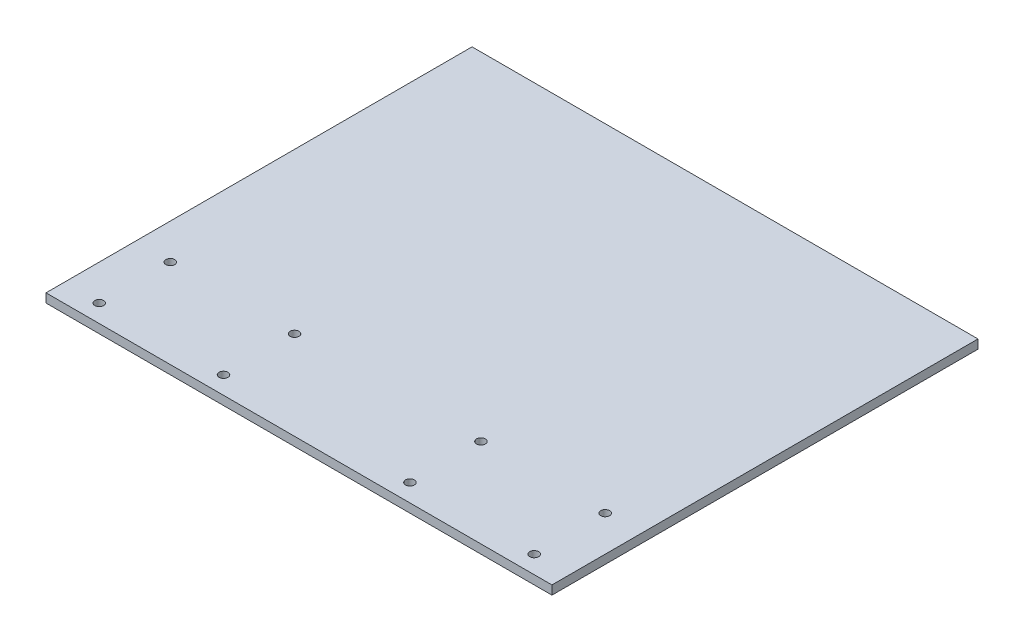
SolidWorks part; units mm, degrees
material "Cast Carbon Steel"
ref_plane "Front Plane" through (0, 0, 0) normal (0, 0, 1) x (1, 0, 0)
ref_plane "Top Plane" through (0, 0, 0) normal (0, 1, 0) x (1, 0, 0)
ref_plane "Right Plane" through (0, 0, 0) normal (1, 0, 0) x (0, 0, -1)
sketch "Sketch1" plane through (0, 0, 0) normal (0, 1, 0) x (1, 0, 0)
  line L1 (-295.5989, 609.6) -> (428.3011, 609.6)
  line L2 (-295.5989, 609.6) -> (-295.5989, 0)
  line L3 (-295.5989, 0) -> (428.3011, 0)
  line L4 (428.3011, 609.6) -> (428.3011, 0)
  dimension "D1" = 723.9
  dimension "D2" = 609.6
  dimension "D4" = 295.5989
extrude "Boss-Extrude1" add sketch "Sketch1" along normal blind 12.7
sketch "Sketch2" plane through (0, 12.7, 0) normal (0, 1, 0) x (1, 0, 0)
  line L0 (428.3011, 0) -> (428.3011, 609.6) construction
  line L1 (66.3511, 609.6) -> (66.3511, 0) construction
  line L2 (428.3011, 609.6) -> (-295.5989, 609.6) construction
  line L3 (-295.5989, 0) -> (428.3011, 0) construction
  circle A0 centre (377.5011, 127) radius 6.35
  circle A1 centre (377.5011, 25.4) radius 6.35
  circle A2 centre (199.7011, 127) radius 6.35
  circle A3 centre (199.7011, 25.4) radius 6.35
  circle A4 centre (-244.7989, 127) radius 6.35
  circle A5 centre (-66.9989, 127) radius 6.35
  circle A6 centre (-244.7989, 25.4) radius 6.35
  circle A7 centre (-66.9989, 25.4) radius 6.35
  dimension "D1" = 12.7
  dimension "D2" = 12.7
  dimension "D3" = 12.7
  dimension "D4" = 12.7
  dimension "D5" = 50.8
  dimension "D6" = 25.4
  dimension "D8" = 177.8
  dimension "D9" = 101.6
extrude "Cut-Extrude1" cut sketch "Sketch2" against normal through all
